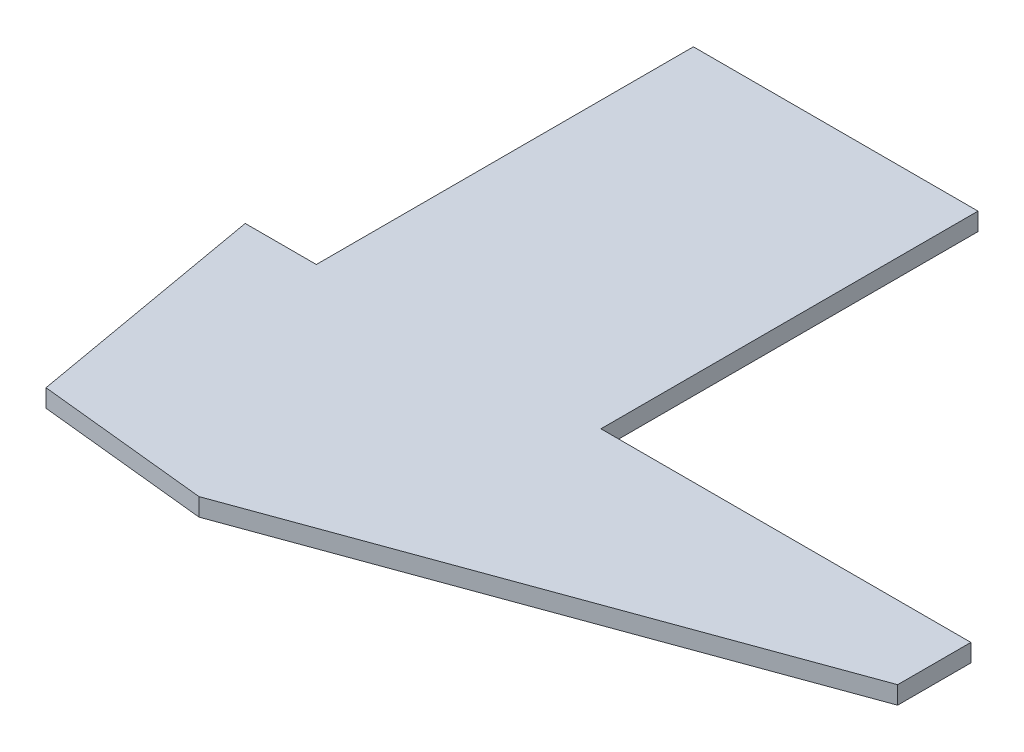
SolidWorks part; units mm, degrees
material "Plywood"
ref_plane "Front Plane" through (0, 0, 0) normal (0, 0, 1) x (1, 0, 0)
ref_plane "Top Plane" through (0, 0, 0) normal (0, 1, 0) x (1, 0, 0)
ref_plane "Right Plane" through (0, 0, 0) normal (1, 0, 0) x (0, 0, -1)
sketch "Sketch2" plane through (0, 0, 0) normal (0, 1, 0) x (1, 0, 0)
  line L0 (50.8, 0) -> (116.84, 0)
  line L2 (0, 0) -> (0, 67.31)
  line L3 (0, 67.31) -> (50.8, 67.31)
  line L4 (50.8, 0) -> (50.8, 67.31)
  line L5 (-55, 0) -> (55, 0) construction
  line L7 (25.4, -46.355) -> (-5.08, -43.18)
  line L8 (-5.08, -43.18) -> (-12.7, 0)
  line L9 (-12.7, 0) -> (0, 0)
  line L11 (25.4, -46.355) -> (116.84, -13.0736)
  line L12 (116.84, -13.0736) -> (116.84, 0)
  dimension "D1" = 50.8
  dimension "D2" = 67.31
  dimension "D3" = 66.04
  dimension "D4" = 12.7
  dimension "D5" = 43.18
  dimension "D6" = 3.175
  dimension "D7" = 7.62
  dimension "D8" = 110
  dimension "D9" = 30.48
extrude "Boss-Extrude1" add sketch "Sketch2" along normal blind 3.175
